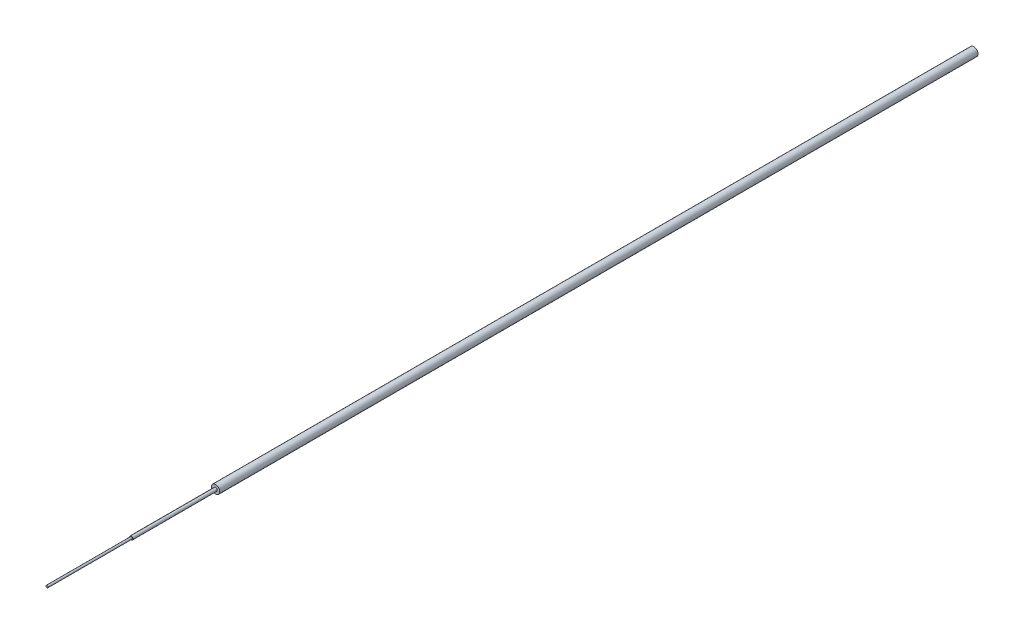
SolidWorks part; units mm, degrees
ref_plane "Front Plane" through (0, 0, 0) normal (0, 0, 1) x (1, 0, 0)
ref_plane "Top Plane" through (0, 0, 0) normal (0, 1, 0) x (1, 0, 0)
ref_plane "Right Plane" through (0, 0, 0) normal (1, 0, 0) x (0, 0, -1)
sketch "Sketch1" plane through (0, 0, 0) normal (0, 0, 1) x (1, 0, 0)
  circle A0 centre (0, 0) radius 0.5
  dimension "D1" = 1
extrude "Boss-Extrude1" add sketch "Sketch1" along normal blind 90
sketch "Sketch2" plane through (0, 0, 90) normal (0, 0, 1) x (1, 0, 0)
  circle A0 centre (0, 0) radius 0.2
  dimension "D1" = 0.4
extrude "Boss-Extrude2" add sketch "Sketch2" along normal blind 10
sketch "Sketch3" plane through (0, 0, 100) normal (0, 0, 1) x (1, 0, 0)
  circle A0 centre (0, 0) radius 0.125
  dimension "D1" = 0.25
extrude "Boss-Extrude3" add sketch "Sketch3" along normal blind 10
